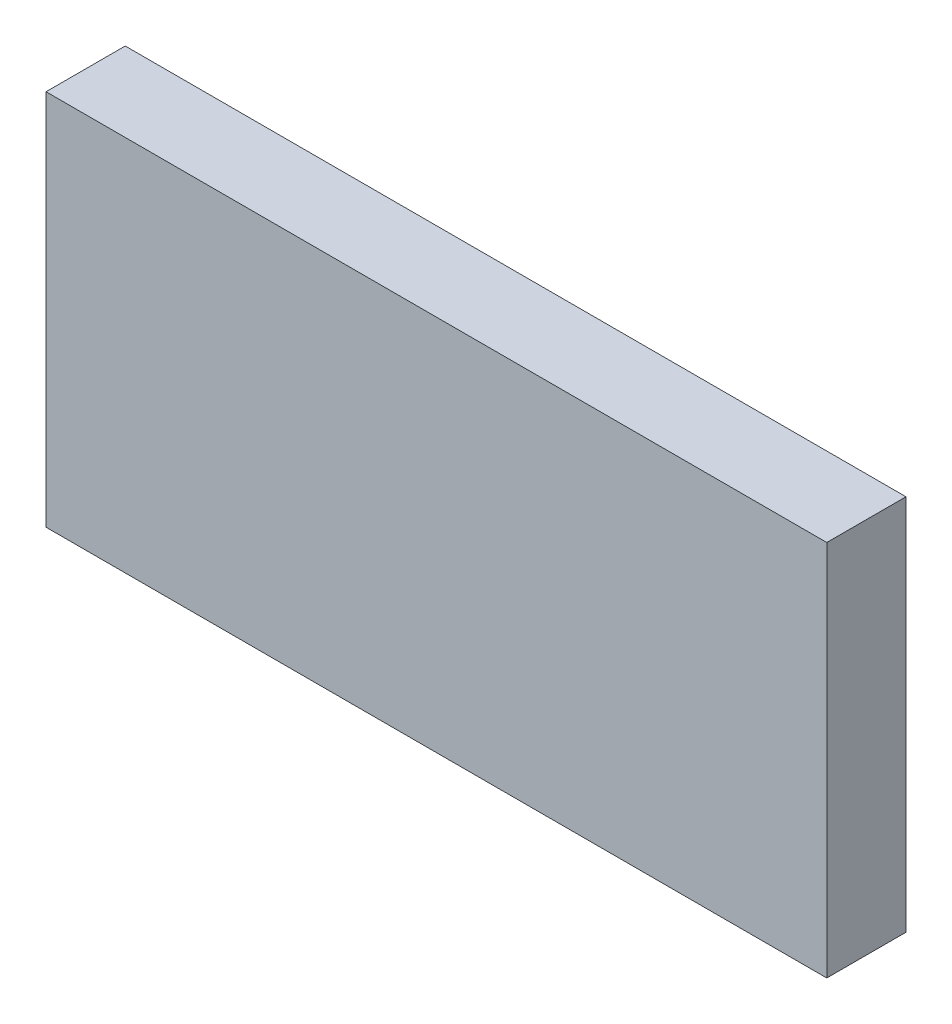
SolidWorks part; units mm, degrees
ref_plane "Front" through (0, 0, 0) normal (0, 0, 1) x (1, 0, 0)
ref_plane "Top" through (0, 0, 0) normal (0, 1, 0) x (1, 0, 0)
ref_plane "Right" through (0, 0, 0) normal (1, 0, 0) x (0, 0, -1)
sketch "Sketch1" plane through (0, 0, 0) normal (0, 0, 1) x (1, 0, 0)
  line L1 (-26.289, -12.7) -> (26.289, -12.7)
  line L2 (-26.289, -12.7) -> (-26.289, 12.7)
  line L3 (-26.289, 12.7) -> (26.289, 12.7)
  line L4 (26.289, -12.7) -> (26.289, 12.7)
  line L5 (-26.289, -12.7) -> (26.289, 12.7) construction
  line L6 (-26.289, 12.7) -> (26.289, -12.7) construction
  point P0 (0, 0)
  dimension "D1" = 52.578
  dimension "D2" = 25.4
extrude "Boss-Extrude1" add sketch "Sketch1" along normal blind 5.334
sketch "Build Plans - Back" [suppressed] plane through (0, 0, 5.334) normal (0, 0, 1) x (1, 0, 0)
  line L0 (26.289, 12.7) -> (26.289, 38.1)
  line L1 (26.289, 38.1) -> (-26.289, 38.1)
  line L2 (-26.289, 38.1) -> (-26.289, 12.7)
  line L4 (26.289, -12.7) -> (26.289, 12.7)
  line L5 (26.289, 12.7) -> (-26.289, 12.7)
  line L6 (-26.289, 12.7) -> (-26.289, -12.7)
  line L7 (-26.289, -12.7) -> (26.289, -12.7)
  line L8 (26.289, -12.7) -> (26.289, 12.7)
  line L9 (26.289, 12.7) -> (-26.289, 12.7)
  line L10 (-26.289, 12.7) -> (-26.289, -12.7)
  line L11 (-26.289, -12.7) -> (26.289, -12.7)
  line L12 (-26.289, 12.7) -> (26.289, 12.7)
  dimension "D1" = 0
  dimension "D2" = 2
sketch "Build Plans - Front" [suppressed] plane through (0, 0, 5.334) normal (0, 0, 1) x (1, 0, 0)
  line L4 (26.289, -12.7) -> (26.289, 12.7)
  line L5 (26.289, 12.7) -> (-26.289, 12.7)
  line L6 (-26.289, 12.7) -> (-26.289, -12.7)
  line L7 (-26.289, -12.7) -> (26.289, -12.7)
  line L8 (26.289, -12.7) -> (26.289, 12.7)
  line L9 (26.289, 12.7) -> (-26.289, 12.7)
  line L10 (-26.289, 12.7) -> (-26.289, -12.7)
  line L11 (-26.289, -12.7) -> (26.289, -12.7)
  dimension "D1" = 0
